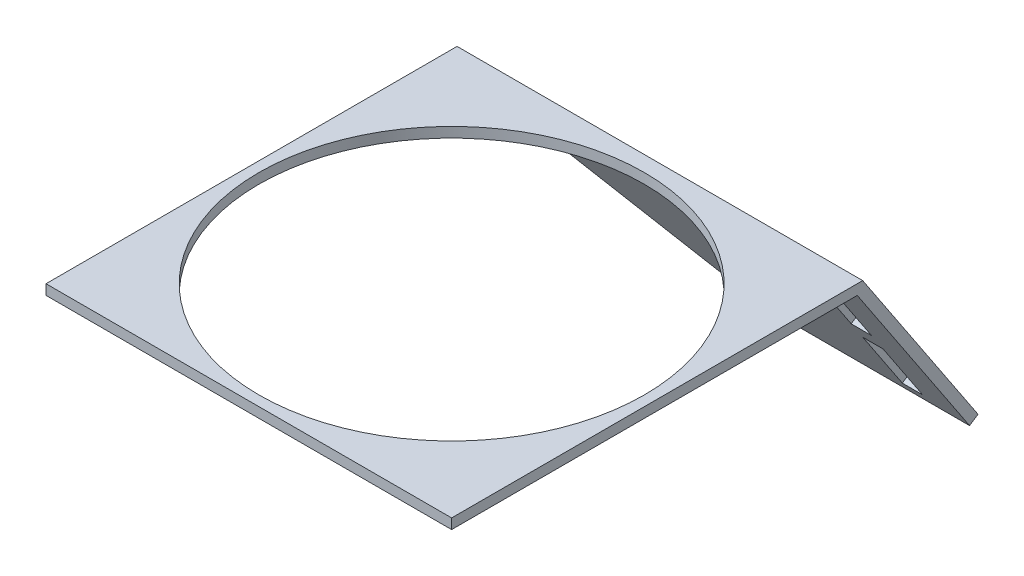
SolidWorks part; units mm, degrees
ref_plane "Front Plane" through (0, 0, 0) normal (0, 0, 1) x (1, 0, 0)
ref_plane "Top Plane" through (0, 0, 0) normal (0, 1, 0) x (1, 0, 0)
ref_plane "Right Plane" through (0, 0, 0) normal (1, 0, 0) x (0, 0, -1)
sketch "Sketch1" plane through (0, 0, 0) normal (0, 1, 0) x (1, 0, 0)
  line L0 (-40, 15.1776) -> (0, -24.8224) construction
  line L1 (-40, 15.1776) -> (0, 15.1776)
  line L2 (-40, 15.1776) -> (-40, -24.8224)
  line L3 (-40, -24.8224) -> (0, -24.8224)
  line L4 (0, 15.1776) -> (0, -24.8224)
  line L5 (0, -24.8224) -> (-0.0735, -24.5293) construction
  circle A0 centre (-20, -4.8224) radius 19
  dimension "D3" = 38
  dimension "D1" = 40
  dimension "D2" = 40
extrude "Boss-Extrude1" add sketch "Sketch1" along normal blind 1
sketch "Sketch2" plane through (0, 0, 0) normal (1, 0, 0) x (0, 0, -1)
  line L0 (15.1776, 0) -> (26.2516, -16.6543)
  line L1 (26.2516, -16.6543) -> (27.0843, -16.1006)
  line L2 (27.0843, -16.1006) -> (15.7136, 1)
  line L3 (15.7136, 1) -> (15.1776, 1)
  line L4 (15.1776, 1) -> (15.1776, 0)
  dimension "D1" = 1
  dimension "D2" = 1
  dimension "D3" = 20
extrude "Boss-Extrude3" add sketch "Sketch2" against normal blind 40
sketch "Sketch3" plane through (0, 6.998, -10.5244) normal (0, -0.5537, 0.8327) x (1, 0, 0)
  line L0 (-20, -28.4038) -> (-40, -8.4038)
  line L1 (-40, -28.4038) -> (0, -28.4038) construction
  line L2 (-40, -8.4038) -> (-40, -28.4038)
  line L3 (-40, -28.4038) -> (-20, -28.4038)
extrude "Cut-Extrude1" cut sketch "Sketch3" against normal blind 40
sketch "Sketch4" plane through (0, 6.998, -10.5244) normal (0, -0.5537, 0.8327) x (1, 0, 0)
  line L0 (-5, -8.4038) -> (-5, -28.4038) construction
  line L1 (0, -8.4038) -> (-40, -8.4038) construction
  line L2 (-20, -28.4038) -> (0, -28.4038) construction
  line L3 (0, -8.4038) -> (0, -28.4038) construction
  line L5 (-4, -27.2711) -> (-6, -27.2711)
  line L6 (-4, -27.2711) -> (-4, -9.3119)
  line L7 (-4, -9.3119) -> (-6, -9.3119)
  line L8 (-6, -27.2711) -> (-6, -9.3119)
  dimension "D1" = 5
  dimension "D2" = 1
  dimension "D3" = 1
extrude "Cut-Extrude2" cut sketch "Sketch4" against normal blind 40
sketch "Sketch5" plane through (0, 6.998, -10.5244) normal (0, -0.5537, 0.8327) x (1, 0, 0)
  line L1 (-3.0456, -20.2228) -> (-7.3369, -20.2228)
  line L2 (-3.0456, -20.2228) -> (-3.0456, -18.1628)
  line L3 (-3.0456, -18.1628) -> (-7.3369, -18.1628)
  line L4 (-7.3369, -20.2228) -> (-7.3369, -18.1628)
extrude "Boss-Extrude4" add sketch "Sketch5" against normal blind 1
